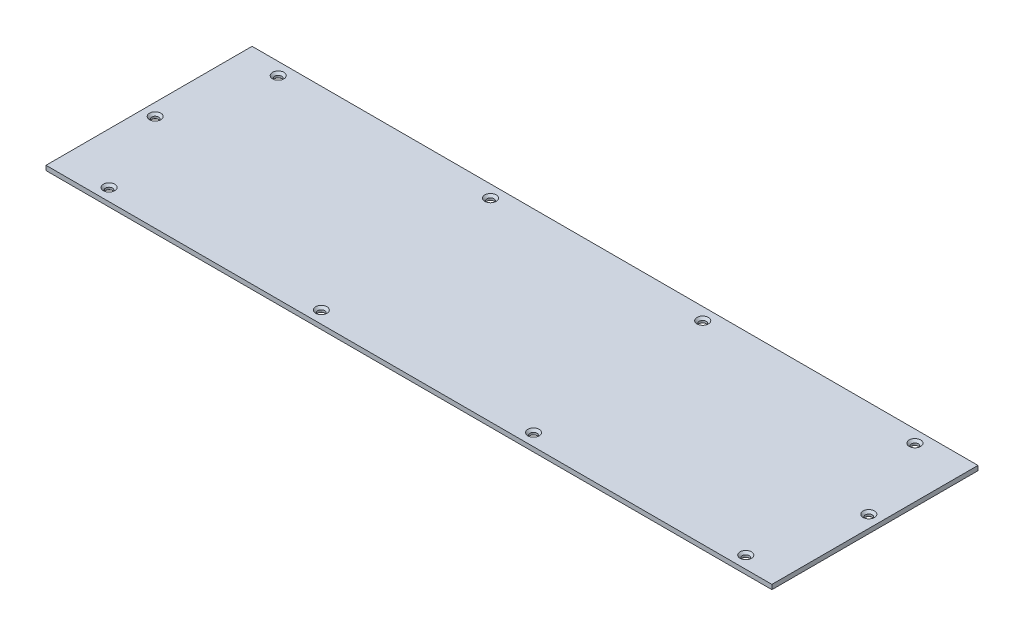
SolidWorks part; units mm, degrees
ref_plane "Спереди" through (0, 0, 0) normal (0, 0, 1) x (1, 0, 0)
ref_plane "Сверху" through (0, 0, 0) normal (0, 1, 0) x (1, 0, 0)
ref_plane "Справа" through (0, 0, 0) normal (1, 0, 0) x (0, 0, -1)
sketch "Эскиз2" plane through (0, 0, 0) normal (0, 1, 0) x (1, 0, 0)
  line L1 (0, 0) -> (472, 0)
  line L2 (0, 0) -> (0, 134)
  line L3 (0, 134) -> (472, 134)
  line L4 (472, 0) -> (472, 134)
  dimension "D1" = 472
  dimension "D2" = 134
extrude "Бобышка-Вытянуть1" add sketch "Эскиз2" along normal blind 3
hole_wizard "Зенковка для винта с потайной головкой M41" positions "Эскиз4" profile "Эскиз3" countersink size "M4" standard "DIN" end condition through all
sketch "Эскиз4" plane through (0, 3, 0) normal (0, 1, 0) x (-1, 0, 0)
  line L0 (0, -134) -> (0, 0) construction
  line L1 (-472, 0) -> (-472, -134) construction
  line L2 (-472, -134) -> (0, -134) construction
  line L3 (0, 0) -> (-472, 0) construction
  point P1 (-25, -126)
  point P4 (-163, -126)
  point P7 (-301, -126)
  point P10 (-439, -126)
  point P13 (-464, -71)
  point P15 (-447, -8)
  point P18 (-309, -8)
  point P21 (-171, -8)
  point P24 (-33, -8)
  point P27 (-8, -63)
  dimension "D1" = 138
  dimension "D2" = 138
  dimension "D3" = 138
  dimension "D4" = 138
  dimension "D5" = 138
  dimension "D6" = 138
  dimension "D7" = 8
  dimension "D8" = 8
  dimension "D9" = 8
  dimension "D10" = 25
  dimension "D11" = 25
  dimension "D12" = 63
  dimension "D13" = 63
  dimension "D14" = 8
sketch "Эскиз3" plane through (25, 3, -126) normal (1, 0, 0) x (0, 0, 1)
  line L0 (0, 0) -> (0, 3)
  line L1 (0, 3) -> (2.4, 3)
  line L2 (2.25, 2.85) -> (2.25, 1.45)
  line L3 (2.25, 1.45) -> (3.7, 0)
  line L5 (3.7, 0) -> (0, 0)
  line L6 (-2.25, 1.45) -> (-3.7, 0) construction
  line L7 (2.4, 3) -> (2.25, 2.85)
  line L8 (-2.4, 3) -> (-2.25, 2.85) construction
  line L11 (0, -6.35) -> (0, 107.95) construction
  dimension "Диаметр сквозного отверстия" = 4.5
  dimension "Глубина сквозного отверстия" = 3
  dimension "Диаметр передней зенковки" = 7.4
  dimension "Угол передней зенковки" = 90
  dimension "Диаметр задней зенковки" = 4.8
  dimension "Угол задней зенковки" = 90
